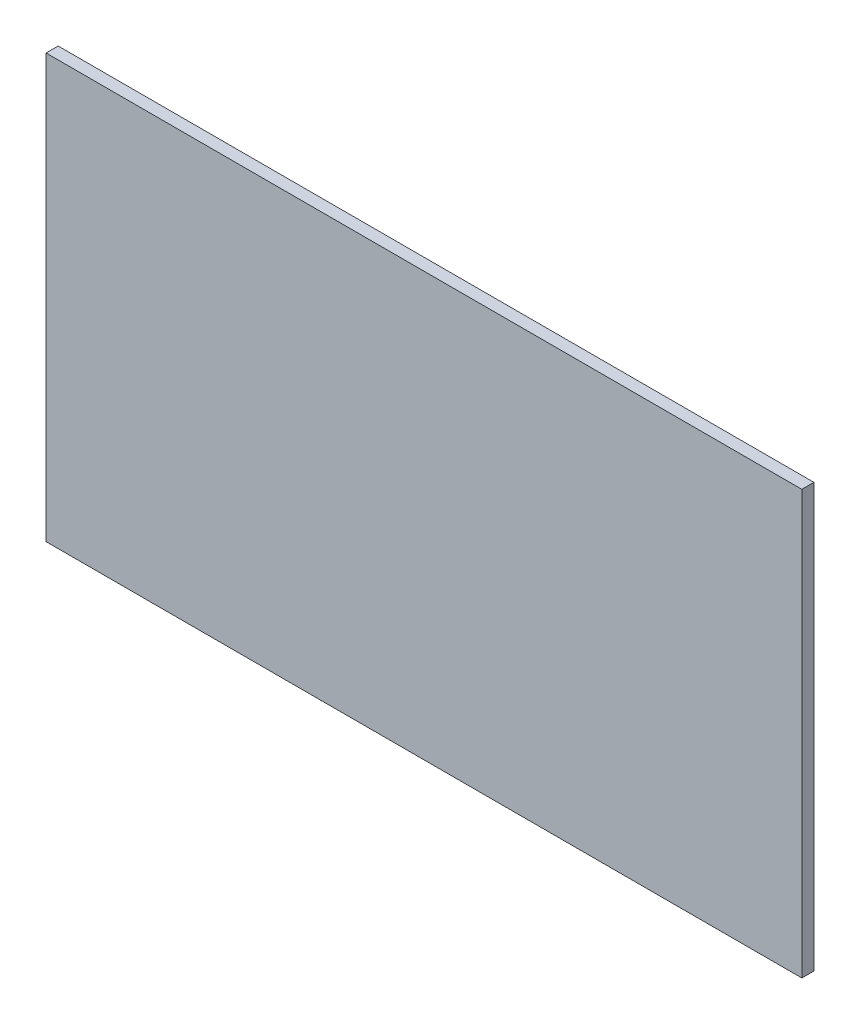
SolidWorks part; units mm, degrees
ref_plane "前视基准面" through (0, 0, 0) normal (0, 0, 1) x (1, 0, 0)
ref_plane "上视基准面" through (0, 0, 0) normal (0, 1, 0) x (1, 0, 0)
ref_plane "右视基准面" through (0, 0, 0) normal (1, 0, 0) x (0, 0, -1)
other "Configuration Table"
sketch "草图1" plane through (0, 0, 0) normal (0, 0, 1) x (1, 0, 0)
  line L1 (-62.2297, 44.2504) -> (187.7703, 44.2504)
  line L2 (-62.2297, 44.2504) -> (-62.2297, -95.7496)
  line L3 (-62.2297, -95.7496) -> (187.7703, -95.7496)
  line L4 (187.7703, 44.2504) -> (187.7703, -95.7496)
  dimension "D1" = 250
  dimension "D2" = 140
extrude "凸台-拉伸1" add sketch "草图1" along normal blind 4
